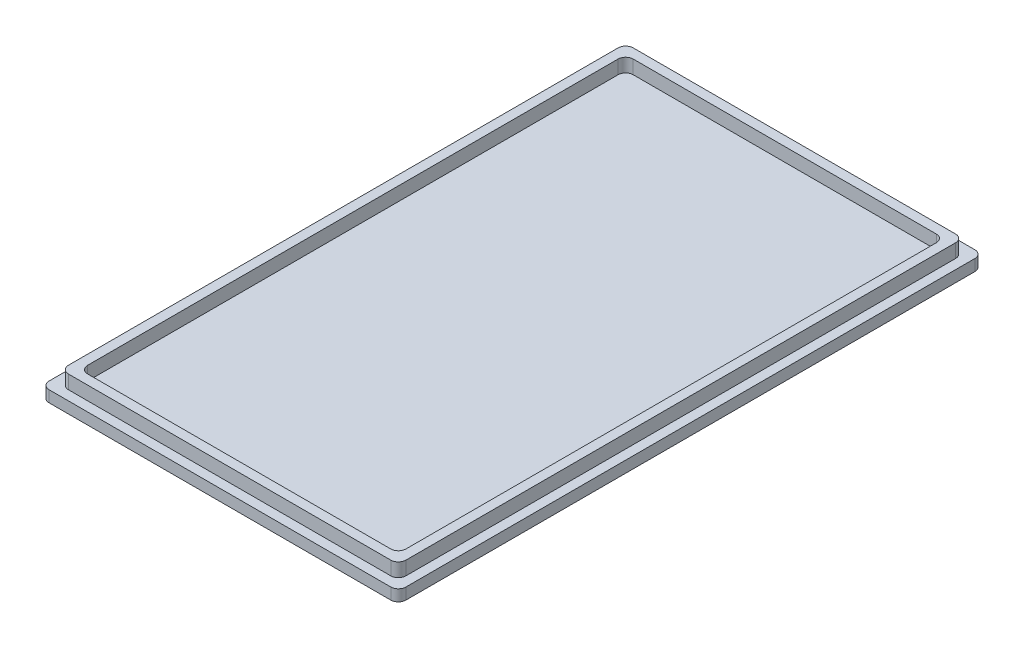
SolidWorks part; units mm, degrees
ref_plane "Front Plane" through (0, 0, 0) normal (0, 0, 1) x (1, 0, 0)
ref_plane "Top Plane" through (0, 0, 0) normal (0, 1, 0) x (1, 0, 0)
ref_plane "Right Plane" through (0, 0, 0) normal (1, 0, 0) x (0, 0, -1)
sketch "Sketch1" plane through (0, 0, 0) normal (0, 1, 0) x (1, 0, 0)
  line L5 (0, 0) -> (47.0912, 0)
  line L6 (0, 0) -> (0, -77.0912)
  line L7 (0, -77.0912) -> (47.0912, -77.0912)
  line L8 (47.0912, 0) -> (47.0912, -77.0912)
extrude "Boss-Extrude1" add sketch "Sketch1" along normal blind 1.5
sketch "Sketch2" plane through (0, 1.5, 0) normal (0, 1, 0) x (1, 0, 0)
  line L3 (1.2728, -1.2728) -> (45.8184, -1.2728)
  line L4 (1.2728, -1.2728) -> (1.2728, -75.8184)
  line L5 (1.2728, -75.8184) -> (45.8184, -75.8184)
  line L6 (45.8184, -1.2728) -> (45.8184, -75.8184)
  line L7 (2.5456, -2.5456) -> (44.5456, -2.5456)
  line L8 (2.5456, -2.5456) -> (2.5456, -74.5456)
  line L9 (2.5456, -74.5456) -> (44.5456, -74.5456)
  line L10 (44.5456, -2.5456) -> (44.5456, -74.5456)
extrude "Boss-Extrude2" add sketch "Sketch2" along normal blind 1.8
fillet "Fillet1" radius 1 12 edges at (2.5456, 2.4, 2.5456) (1.2728, 2.4, 1.2728) (0, 0.75, 0) (2.5456, 2.4, 74.5456) (1.2728, 2.4, 75.8184) (0, 0.75, 77.0912) (44.5456, 2.4, 74.5456) (47.0912, 0.75, 77.0912) (45.8184, 2.4, 75.8184) (44.5456, 2.4, 2.5456) (47.0912, 0.75, 0) (45.8184, 2.4, 1.2728)
sketch "Sketch3" plane through (0, 0, 0) normal (0, -1, 0) x (1, 0, 0)
  line L0 (23.5456, 77.0912) -> (23.5456, 0)
  line L1 (11.5456, 70.5428) -> (35.5456, 70.5428)
  line L2 (11.5456, 70.5428) -> (11.5456, 6.5428)
  line L3 (11.5456, 6.5428) -> (35.5456, 6.5428)
  line L4 (35.5456, 70.5428) -> (35.5456, 6.5428)
  line L5 (1, 77.0912) -> (46.0912, 77.0912) construction
  line L6 (46.0912, 0) -> (1, 0) construction
  line L7 (0, 38.5456) -> (47.0912, 38.5456)
  line L8 (0, 1) -> (0, 76.0912) construction
  line L9 (47.0912, 76.0912) -> (47.0912, 1) construction
extrude "Boss-Extrude3" add sketch "Sketch3" along normal blind 10 contours L2 L3 L4 L1
sketch "Sketch4" plane through (11.5456, 0, 0) normal (-1, 0, 0) x (0, 0, 1)
  line L1 (70.5428, 0) -> (6.5428, 0) construction
  line L3 (14.5428, 0) -> (62.5428, 0)
  line L4 (14.5428, 0) -> (14.5428, -6)
  line L5 (14.5428, -6) -> (62.5428, -6)
  line L6 (62.5428, 0) -> (62.5428, -6)
extrude "Cut-Extrude1" cut sketch "Sketch4" against normal blind 24
fillet "Fillet2" radius 6 2 edges at (23.5456, -10, 70.5428) (23.5456, -10, 6.5428)
fillet "Fillet3" radius 1 2 edges at (23.5456, -6, 62.5428) (23.5456, -6, 14.5428)
